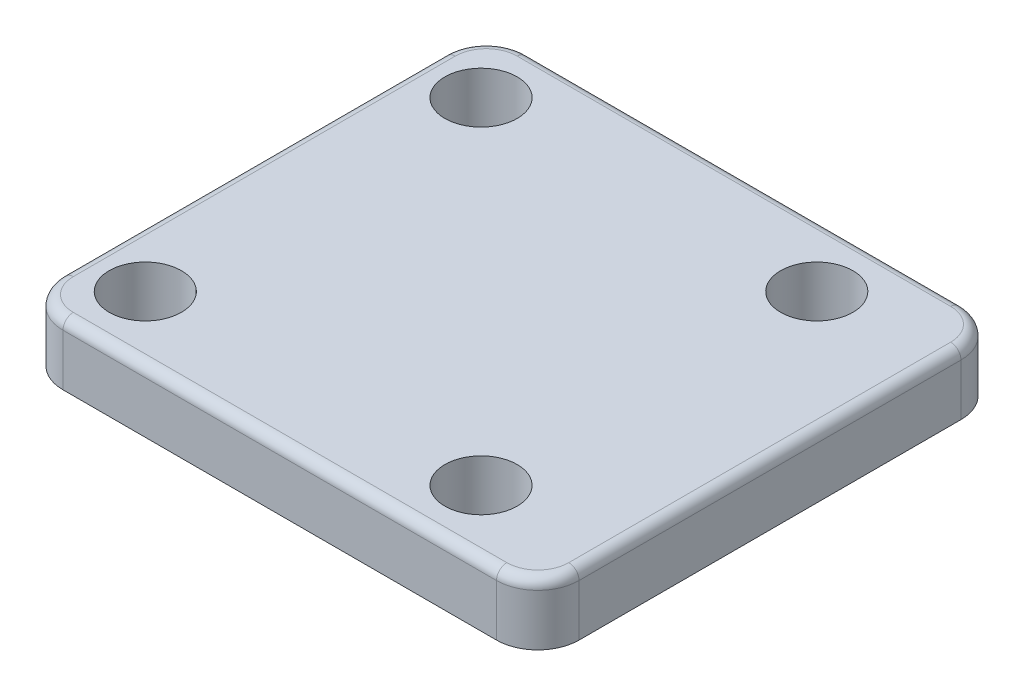
SolidWorks part; units mm, degrees
material "6061 Alloy"
ref_plane "Front Plane" through (0, 0, 0) normal (0, 0, 1) x (1, 0, 0)
ref_plane "Top Plane" through (0, 0, 0) normal (0, 1, 0) x (1, 0, 0)
ref_plane "Right Plane" through (0, 0, 0) normal (1, 0, 0) x (0, 0, -1)
sketch "Sketch1" plane through (0, 0, 0) normal (0, 1, 0) x (1, 0, 0)
  line L1 (28, -22.5) -> (-22, -22.5)
  line L2 (28, -22.5) -> (28, 22.5)
  line L3 (28, 22.5) -> (-22, 22.5)
  line L4 (-22, -22.5) -> (-22, 22.5)
  line L5 (28, -22.5) -> (-22, 22.5) construction
  line L6 (28, 22.5) -> (-22, -22.5) construction
  point P0 (3, 0)
  dimension "D1" = 45
  dimension "D2" = 50
  dimension "D3" = 22
extrude "Body" add sketch "Sketch1" along normal blind 6
sketch "Sketch4" plane through (0, 0, 0) normal (0, -1, 0) x (1, 0, 0)
  circle A0 centre (0, 0) radius 16
  dimension "D1" = 32
extrude "Round" add sketch "Sketch4" along normal blind 2
chamfer "1x45 Chamfer" distance 1 angle 45 1 edges at (0, -2, -16)
sketch "Sketch5" plane through (0, 0, 0) normal (0, -1, 0) x (1, 0, 0)
  line L0 (0, 0) -> (0, 23) construction
  line L1 (0, 0) -> (16.2635, 16.2635) construction
  circle A0 centre (0, 0) radius 23 construction
  circle A1 centre (16.2635, 16.2635) radius 3.5
  dimension "D1" = 46
  dimension "D3" = 7
  dimension "D2" = 45
extrude "Hole 1" cut sketch "Sketch5" against normal through all
pattern_circular "Holes 2-4" count 4 over 360 about axis through (0, 0, 0) along (0, 1, 0) of "Hole 1"
fillet "R4 Fillets" radius 4 4 edges at (-22, 3, -22.5) (28, 3, -22.5) (-22, 3, 22.5) (28, 3, 22.5)
fillet "R1 Fillet" radius 1 8 edges at (26.8284, 6, 21.3284) (3, 6, 22.5) (-20.8284, 6, 21.3284) (-22, 6, 0) (-20.8284, 6, -21.3284) (3, 6, -22.5) (26.8284, 6, -21.3284) (28, 6, 0)
